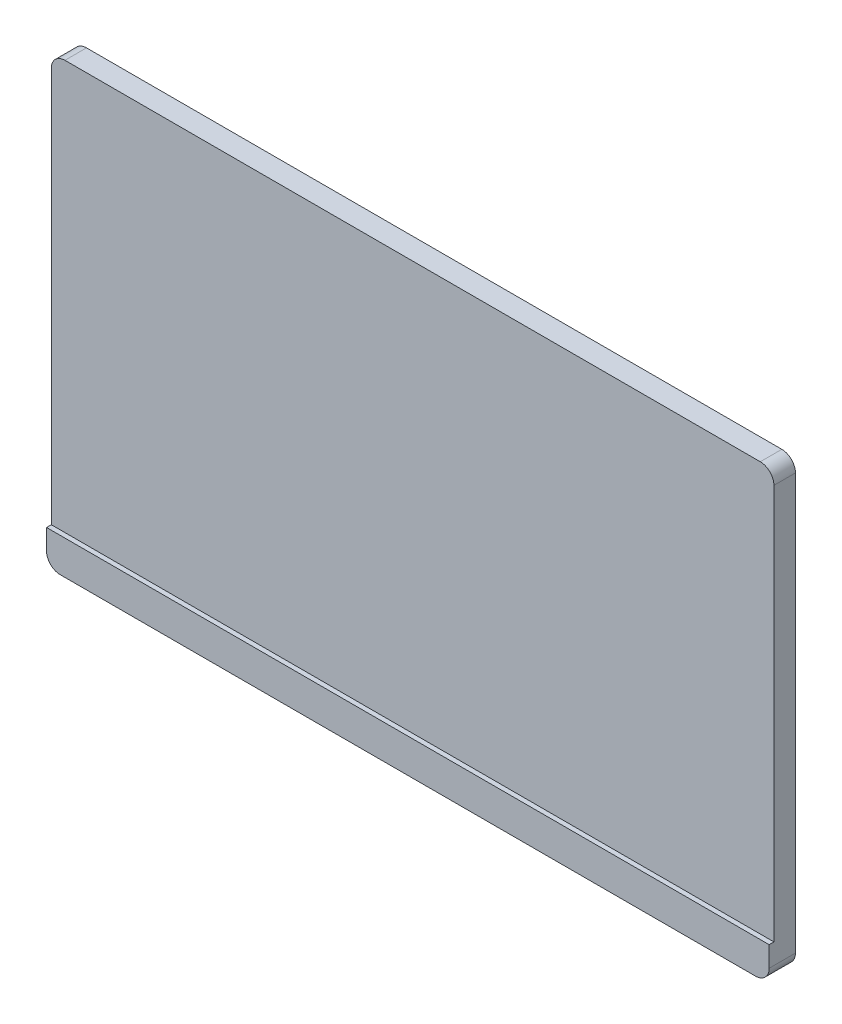
SolidWorks part; units mm, degrees
ref_plane "Plano frontal" through (0, 0, 0) normal (0, 0, 1) x (1, 0, 0)
ref_plane "Plano superior" through (0, 0, 0) normal (0, 1, 0) x (1, 0, 0)
ref_plane "Plano direito" through (0, 0, 0) normal (1, 0, 0) x (0, 0, -1)
sketch "Esboço1" plane through (0, 0, 0) normal (0, 0, 1) x (1, 0, 0)
  line L1 (0, 0) -> (530, 0)
  line L2 (0, 0) -> (0, 325)
  line L3 (0, 325) -> (530, 325)
  line L4 (530, 0) -> (530, 325)
  dimension "D1" = 530
  dimension "D2" = 325
extrude "Ressalto-extrusão1" add sketch "Esboço1" along normal blind 15.8
sketch "Esboço2" plane through (0, 0, 15.8) normal (0, 0, 1) x (1, 0, 0)
  line L0 (530, 0) -> (530, 325) construction
  line L1 (0, 0) -> (530, 0)
  line L2 (0, 0) -> (0, 25)
  line L3 (0, 25) -> (530, 25)
  line L4 (530, 0) -> (530, 25)
  dimension "D1" = 25
extrude "Ressalto-extrusão2" add sketch "Esboço2" along normal blind 3.5
sketch "Esboço3" plane through (0, 0, 0) normal (0, 0, -1) x (-1, 0, 0)
  line L0 (-530, 0) -> (-530, 325) construction
  line L1 (-530, 220) -> (0, 220)
  line L2 (-530, 220) -> (-530, 0)
  line L3 (-530, 0) -> (0, 0)
  line L4 (0, 220) -> (0, 0)
  dimension "D1" = 220
extrude "Ressalto-extrusão3" add sketch "Esboço3" along normal blind 30
sketch "Esboço4" plane through (0, 220, 0) normal (0, 1, 0) x (1, 0, 0)
  line L0 (530, 0) -> (530, 30)
  line L1 (530, 30) -> (420, 30)
  line L2 (0, 30) -> (530, 30) construction
  arc A0 (530, 0) -> (475, 14.4997) centre (530, 111.5624) cw
  arc A1 (475, 14.4997) -> (420, 30) centre (415.9439, -89.7211) ccw
  point P10 (0, 0)
  point P11 (480.4596, 11.6028)
  dimension "D1" = 110
  dimension "D2" = 55
extrude "Corte-extrusão1" cut sketch "Esboço4" against normal through all
sketch "Esboço6" plane through (0, 220, 0) normal (0, 1, 0) x (1, 0, 0)
  line L0 (0, 0) -> (0, 30)
  line L1 (0, 30) -> (110, 30)
  line L2 (0, 30) -> (420, 30) construction
  arc A0 (0, 0) -> (55, 15) centre (0, 108.3333) ccw
  arc A1 (55, 15) -> (110, 30) centre (110, -78.3333) cw
  dimension "D1" = 110
  dimension "D2" = 55
extrude "Corte-extrusão2" cut sketch "Esboço6" against normal through all
fillet "Filete2" radius 10 4 edges at (530, 0, 9.65) (0, 0, 9.65) (0, 325, 7.9) (530, 325, 7.9)
